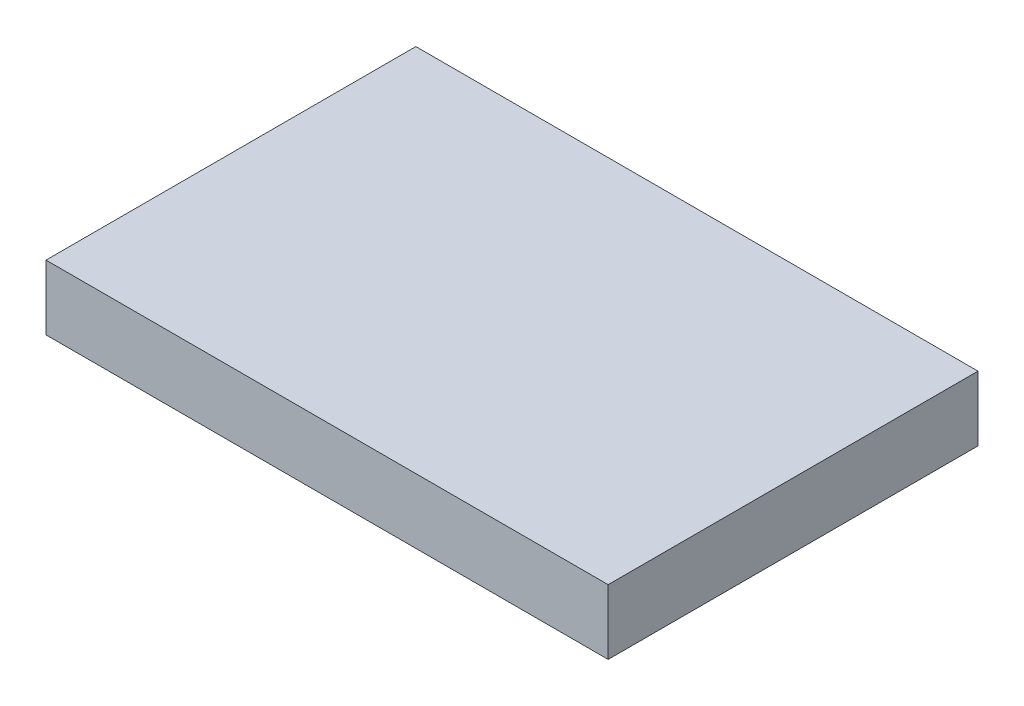
SolidWorks part; units mm, degrees
ref_plane "Front Plane" through (0, 0, 0) normal (0, 0, 1) x (1, 0, 0)
ref_plane "Top Plane" through (0, 0, 0) normal (0, 1, 0) x (1, 0, 0)
ref_plane "Right Plane" through (0, 0, 0) normal (1, 0, 0) x (0, 0, -1)
sketch "Sketch1" plane through (0, 0, 0) normal (0, 1, 0) x (1, 0, 0)
  line L1 (0, 0) -> (82.46, 0)
  line L2 (0, 0) -> (0, -54.25)
  line L3 (0, -54.25) -> (82.46, -54.25)
  line L4 (82.46, 0) -> (82.46, -54.25)
  dimension "D1" = 82.46
  dimension "D2" = 54.25
extrude "Boss-Extrude1" add sketch "Sketch1" along normal blind 9.5
